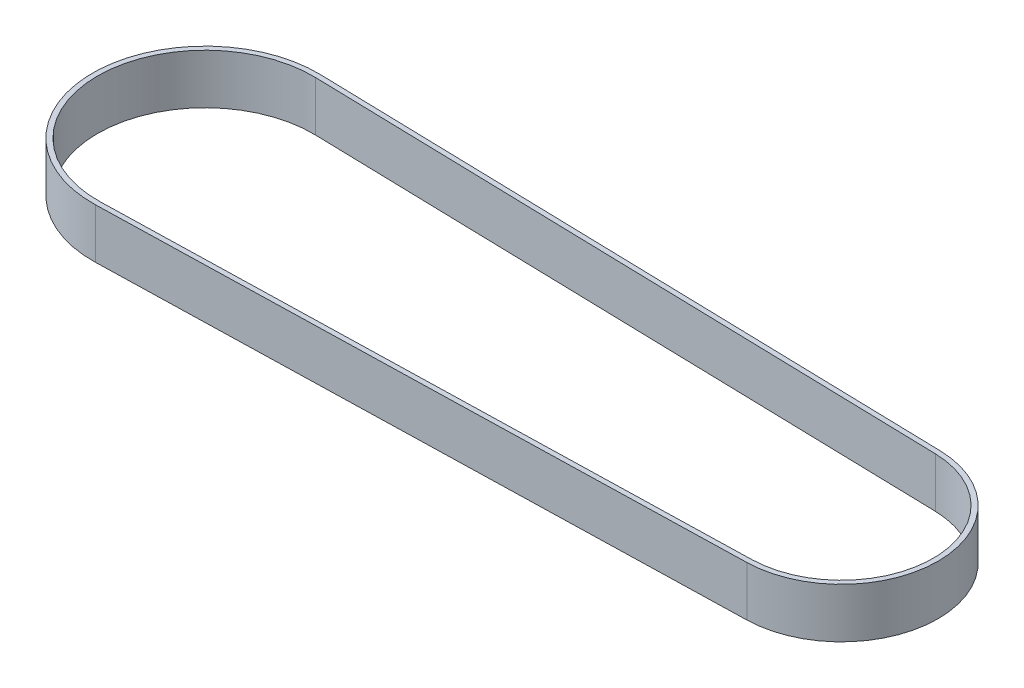
SolidWorks part; units mm, degrees
material "BUTYL"
ref_plane "Front Plane" through (0, 0, 0) normal (0, 0, 1) x (1, 0, 0)
ref_plane "Top Plane" through (0, 0, 0) normal (0, 1, 0) x (1, 0, 0)
ref_plane "Right Plane" through (0, 0, 0) normal (1, 0, 0) x (0, 0, -1)
sketch "Sketch1" plane through (0, 0, 0) normal (0, 1, 0) x (1, 0, 0)
  line L0 (0, 0) -> (127.63, 0) construction
  line L1 (0.5416, 21.5932) -> (128.0913, 18.3942)
  line L2 (0.5666, 22.5929) -> (128.1164, 19.3939)
  line L3 (0.5666, -22.5929) -> (128.1164, -19.3939)
  line L4 (0.5416, -21.5932) -> (128.0913, -18.3942)
  arc A0 (0.5416, 21.5932) -> (0.5416, -21.5932) centre (0, 0) ccw
  arc A1 (128.0913, -18.3942) -> (128.0913, 18.3942) centre (127.63, 0) ccw
  arc A2 (128.1164, -19.3939) -> (128.1164, 19.3939) centre (127.63, 0) ccw
  arc A3 (0.5666, 22.5929) -> (0.5666, -22.5929) centre (0, 0) ccw
  dimension "D1" = 43.2
  dimension "D3" = 36.8
  dimension "D2" = 127.63
  dimension "D4" = 1
extrude "Boss-Extrude1" add sketch "Sketch1" along normal blind 10
